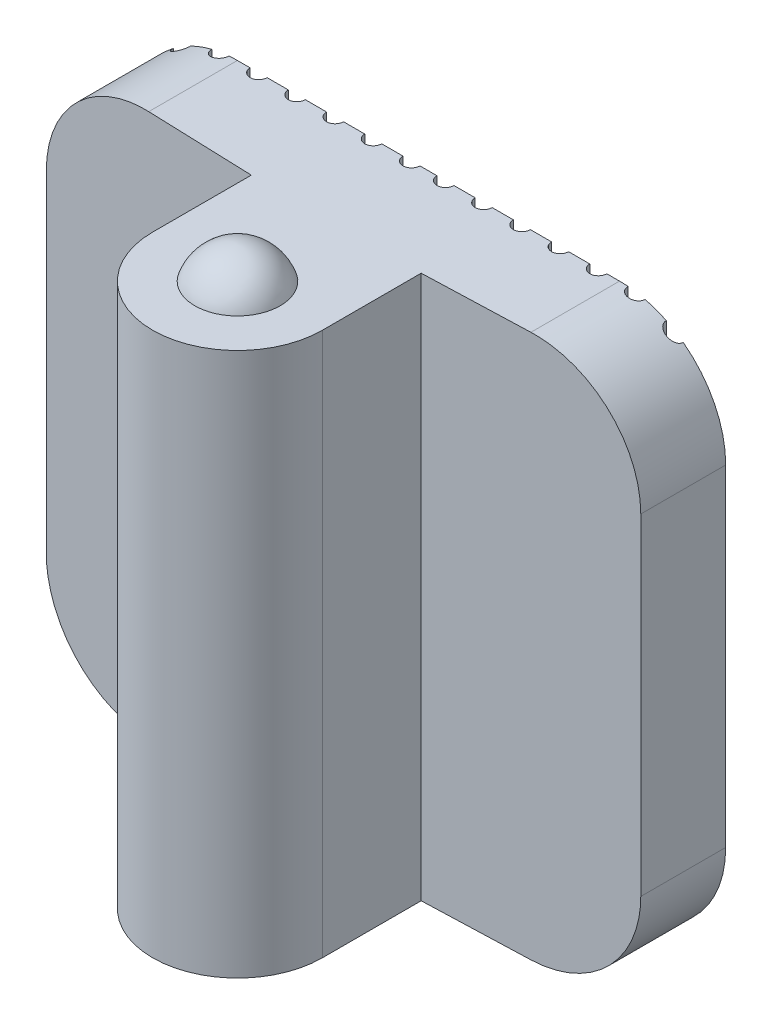
SolidWorks part; units mm, degrees
ref_plane "Front Plane" through (0, 0, 0) normal (0, 0, 1) x (1, 0, 0)
ref_plane "Top Plane" through (0, 0, 0) normal (0, 1, 0) x (1, 0, 0)
ref_plane "Right Plane" through (0, 0, 0) normal (1, 0, 0) x (0, 0, -1)
sketch "Sketch1" plane through (0, 0, 0) normal (0, 0, 1) x (1, 0, 0)
  line L1 (0, 0) -> (14, 0)
  line L2 (0, 0) -> (0, 12.8)
  line L3 (0, 12.8) -> (14, 12.8)
  line L4 (14, 0) -> (14, 12.8)
  dimension "D1" = 14
  dimension "D2" = 12.8
extrude "Boss-Extrude1" add sketch "Sketch1" along normal blind 2
sketch "Sketch2" plane through (0, 0, 0) normal (0, -1, 0) x (1, 0, 0)
  line L0 (0, 2) -> (5.0026, 2.1747)
  line L1 (0, 2) -> (14, 2) construction
  line L2 (5.0026, 2) -> (5.0026, 4.5)
  line L3 (9.0026, 2) -> (9.0026, 4.5)
  line L4 (14, 2) -> (9.0026, 2.1745)
  line L5 (0, 0) -> (14, 0) construction
  line L6 (5.0026, 2) -> (9.0026, 2)
  line L7 (0, 2) -> (14, 2)
  arc A0 (5.0026, 4.5) -> (9.0026, 4.5) centre (7.0026, 4.5) cw
  line M8 (14, 2) -> (0, 2)
  dimension "D3" = 4.5
  dimension "D1" = 2
  dimension "D2" = 2
  dimension "D4" = 4
extrude "Boss-Extrude3" add sketch "Sketch2" against normal blind 12.8 contours L2 L0 M8 | A0 L2 L3 M8 | L4 L3 M8
sketch "Sketch3" plane through (0, 0, 0) normal (0, -1, 0) x (1, 0, 0)
  line L0 (0, 0) -> (14, 0) construction
  line L1 (7, 0) -> (7, 4.9514) construction
  line L2 (0.2, 0) -> (14, 0)
  line L3 (13, 0) -> (1, 0)
  arc A1 (1, 0) -> (1.4, 0) centre (1.2, 0) cw
  arc A2 (1.9, 0) -> (2.3, 0) centre (2.1, 0) cw
  arc A3 (2.8, 0) -> (3.2, 0) centre (3, 0) cw
  arc A4 (3.7, 0) -> (4.1, 0) centre (3.9, 0) cw
  arc A5 (4.6, 0) -> (5, 0) centre (4.8, 0) cw
  arc A6 (5.5, 0) -> (5.9, 0) centre (5.7, 0) cw
  arc A7 (6.4, 0) -> (6.8, 0) centre (6.6, 0) cw
  arc A8 (7.6, 0) -> (7.2, 0) centre (7.4, 0) ccw
  arc A9 (8.5, 0) -> (8.1, 0) centre (8.3, 0) ccw
  arc A10 (9.4, 0) -> (9, 0) centre (9.2, 0) ccw
  arc A11 (10.3, 0) -> (9.9, 0) centre (10.1, 0) ccw
  arc A12 (11.2, 0) -> (10.8, 0) centre (11, 0) ccw
  arc A13 (12.1, 0) -> (11.7, 0) centre (11.9, 0) ccw
  arc A14 (13, 0) -> (12.6, 0) centre (12.8, 0) ccw
  dimension "D4" = 0.2
  dimension "D5" = 0.2
  dimension "D6" = 0.2
  dimension "D7" = 0.2
  dimension "D8" = 0.2
  dimension "D9" = 0.2
  dimension "D16" = 0.2
  dimension "D2" = 0.2
  dimension "D10" = 0.5
  dimension "D11" = 0.5
  dimension "D12" = 0.5
  dimension "D13" = 0.5
  dimension "D14" = 0.5
  dimension "D15" = 0.5
extrude "Cut-Extrude1" cut sketch "Sketch3" against normal blind 14 and the other way through all contours L2 A14 | L2 A13 | L2 A12 | L2 A11 | L2 A10 | L2 A9 | L2 A8 | A7 L2 | A6 L2 | A5 L2 | A4 L2 | A3 L2 | A2 L2 | A1 L2
fillet "Fillet3" radius 2.5 1 edges at (0, 0, 1)
fillet "Fillet4" radius 2.5 3 edges at (0, 12.8, 1) (14, 12.8, 1) (14, 0, 1)
sketch "Sketch4" plane through (0, 0, 0) normal (0, -1, 0) x (1, 0, 0)
  line L0 (7.0026, 6.5) -> (7.0026, 0.9612) construction
  line L1 (6.8, 0) -> (7.2, 0) construction
  arc A0 (9.0026, 4.5) -> (5.0026, 4.5) centre (7.0026, 4.5) ccw construction
  circle A1 centre (7.0026, 4.5) radius 1
  dimension "D1" = 2
  dimension "D2" = 4.5
ref_plane "Plane1" through (7.0026, 0, 0) normal (1, 0, 0) x (0, 0, -1)
sketch "Sketch5" plane through (7.0026, 0, 0) normal (1, 0, 0) x (0, 0, -1)
  line L0 (-4.5, 0) -> (-4.5, -0.75)
  dimension "D1" = 0.75
sketch "Sketch8" plane through (7.0026, 0, 0) normal (1, 0, 0) x (0, 0, -1)
  line L0 (-5.5008, 0) -> (-4.5, 0)
  line L2 (-4.5, -0.75) -> (-4.5, 0) construction
  line L3 (-4.5, -0.75) -> (-4.5, 0)
  arc A0 (-5.5008, 0) -> (-4.5, -0.75) centre (-4.4897, 0.3065) ccw
revolve "Revolve3" add sketch "Sketch8" angle 360 about L2
sketch "Sketch10" plane through (0, 12.8, 0) normal (0, 1, 0) x (1, 0, 0)
  line L0 (7.0026, -6.5) -> (7.0026, -0.8306) construction
  line L1 (12.6, 0) -> (12.1, 0) construction
  arc A0 (5.0026, -4.5) -> (9.0026, -4.5) centre (7.0026, -4.5) ccw construction
  circle A1 centre (7.0026, -4.5) radius 1
  dimension "D1" = 2
  dimension "D2" = 4.5
sketch "Sketch11" plane through (7.0026, 0, 0) normal (1, 0, 0) x (0, 0, -1)
  line L0 (-4.5, 12.8) -> (-4.5, 13.55) construction
  line L1 (-6.5, 12.8) -> (-0.8306, 12.8) construction
  line L2 (-3.4952, 12.8) -> (-4.5, 12.8)
  line L3 (-4.5, 12.8) -> (-4.5, 13.55)
  arc A0 (-4.5, 13.55) -> (-3.4952, 12.8) centre (-4.5317, 12.4594) cw
  dimension "D1" = 0.75
revolve "Revolve4" add sketch "Sketch11" angle 360 about L0
